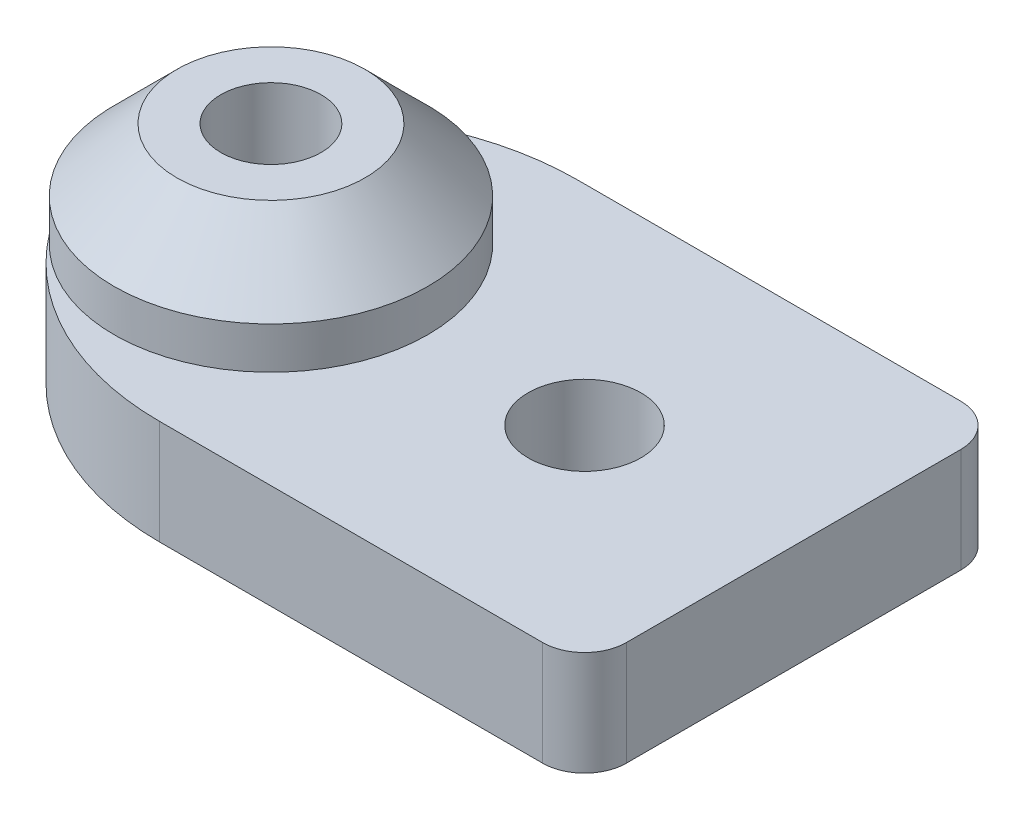
SolidWorks part; units mm, degrees
ref_plane "Front Plane" through (0, 0, 0) normal (0, 0, 1) x (1, 0, 0)
ref_plane "Top Plane" through (0, 0, 0) normal (0, 1, 0) x (1, 0, 0)
ref_plane "Right Plane" through (0, 0, 0) normal (1, 0, 0) x (0, 0, -1)
sketch "Sketch1" plane through (0, 0, 0) normal (0, 1, 0) x (1, 0, 0)
  line L0 (4.668, 0) -> (25, 0)
  line L1 (0, 0) -> (25, 0) construction
  line L2 (0, 0) -> (0, 20) construction
  line L3 (0, 20) -> (25, 20) construction
  line L4 (25, 0) -> (25, 20)
  line L5 (4.668, 20) -> (25, 20)
  arc A0 (-6.2428, 14.1566) -> (-6.2428, 5.8434) centre (0, 10) ccw
  arc A1 (4.668, 20) -> (-6.2428, 14.1566) centre (4.668, 6.892) ccw
  arc A2 (-6.2428, 5.8434) -> (4.668, 0) centre (4.668, 13.108) ccw
  circle A3 centre (15, 10) radius 2.7
  circle A4 centre (0, 10) radius 2.4
  dimension "D1" = 15
  dimension "D4" = 25
  dimension "D5" = 26.216
  dimension "D6" = 26.216
  dimension "D7" = 10
  dimension "D8" = 4.8
  dimension "D9" = 5.4
  dimension "D10" = 25
  dimension "D11" = 10
  dimension "D12" = 10
  dimension "D13" = 10
  dimension "D2" = 20
  dimension "D3" = 25
extrude "Boss-Extrude1" add sketch "Sketch1" along normal blind 5
sketch "Sketch2" plane through (0, 5, 0) normal (0, 1, 0) x (1, 0, 0)
  circle A0 centre (0, 10) radius 7.5
  circle A1 centre (0, 10) radius 2.4
  dimension "D1" = 15
  dimension "D2" = 4.8
extrude "Boss-Extrude2" add sketch "Sketch2" along normal blind 5
chamfer "Chamfer1" distance 3 angle 45 1 edges at (0, 10, -2.5)
fillet "Fillet1" radius 2 2 edges at (25, 2.5, -20) (25, 2.5, 0)
